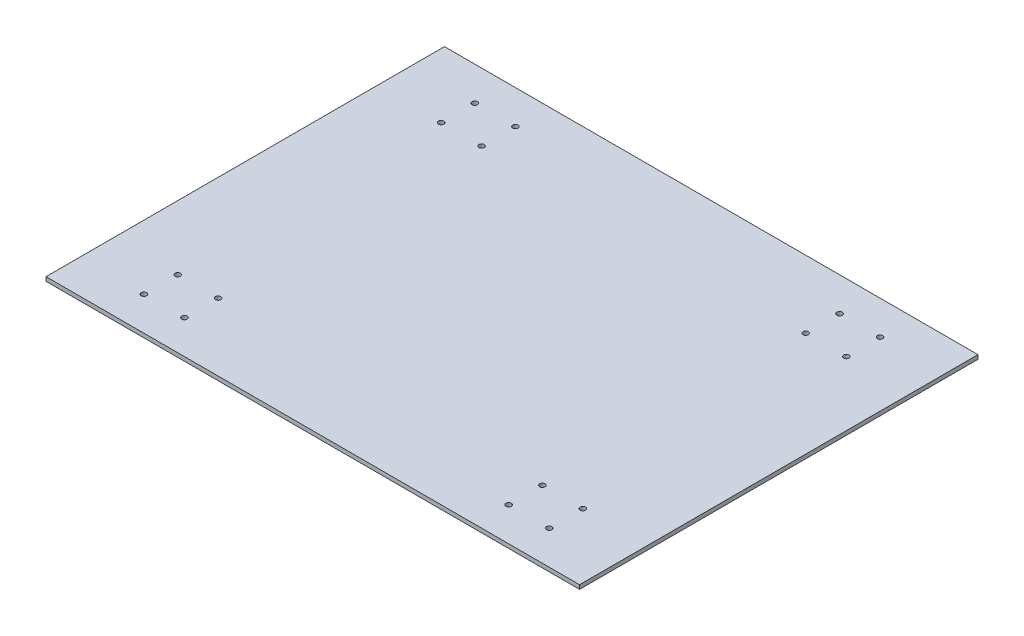
SolidWorks part; units mm, degrees
ref_plane "Front Plane" through (0, 0, 0) normal (0, 0, 1) x (1, 0, 0)
ref_plane "Top Plane" through (0, 0, 0) normal (0, 1, 0) x (1, 0, 0)
ref_plane "Right Plane" through (0, 0, 0) normal (1, 0, 0) x (0, 0, -1)
sketch "Sketch1" plane through (0, 0, 0) normal (0, 1, 0) x (1, 0, 0)
  line L1 (-197.5, 147.5) -> (197.5, 147.5)
  line L2 (-197.5, 147.5) -> (-197.5, -147.5)
  line L3 (-197.5, -147.5) -> (197.5, -147.5)
  line L4 (197.5, 147.5) -> (197.5, -147.5)
  line L5 (-197.5, 147.5) -> (197.5, -147.5) construction
  line L6 (-197.5, -147.5) -> (197.5, 147.5) construction
  point P0 (0, 0)
  dimension "D1" = 295
  dimension "D2" = 395
extrude "Boss-Extrude1" add sketch "Sketch1" along normal blind 3
sketch "Sketch2" plane through (0, 3, 0) normal (0, 1, 0) x (1, 0, 0)
  circle A0 centre (150, -122.5) radius 2
  circle A1 centre (120, -122.5) radius 2
  circle A2 centre (150, -97.5) radius 2
  circle A3 centre (120, -97.5) radius 2
  circle A4 centre (150, 97.5) radius 2
  circle A5 centre (120, 97.5) radius 2
  circle A6 centre (150, 122.5) radius 2
  circle A7 centre (120, 122.5) radius 2
  circle A8 centre (-120, -122.5) radius 2
  circle A9 centre (-150, -122.5) radius 2
  circle A10 centre (-120, -97.5) radius 2
  circle A11 centre (-150, -97.5) radius 2
  circle A12 centre (-120, 97.5) radius 2
  circle A13 centre (-150, 97.5) radius 2
  circle A14 centre (-120, 122.5) radius 2
  circle A15 centre (-150, 122.5) radius 2
  dimension "D1" = 4
  dimension "D3" = 25
  dimension "D4" = 30
  dimension "D6" = 4
  dimension "D10" = 4
  dimension "D13" = 4
  dimension "D17" = 97.5
  dimension "D2" = 97.5
  dimension "D5" = 120
  dimension "D7" = 25
  dimension "D8" = 30
  dimension "D9" = 97.5
  dimension "D11" = 25
  dimension "D12" = 30
  dimension "D14" = 25
  dimension "D15" = 30
  dimension "D16" = 97.5
  dimension "D18" = 120
extrude "Cut-Extrude1" cut sketch "Sketch2" against normal through all
